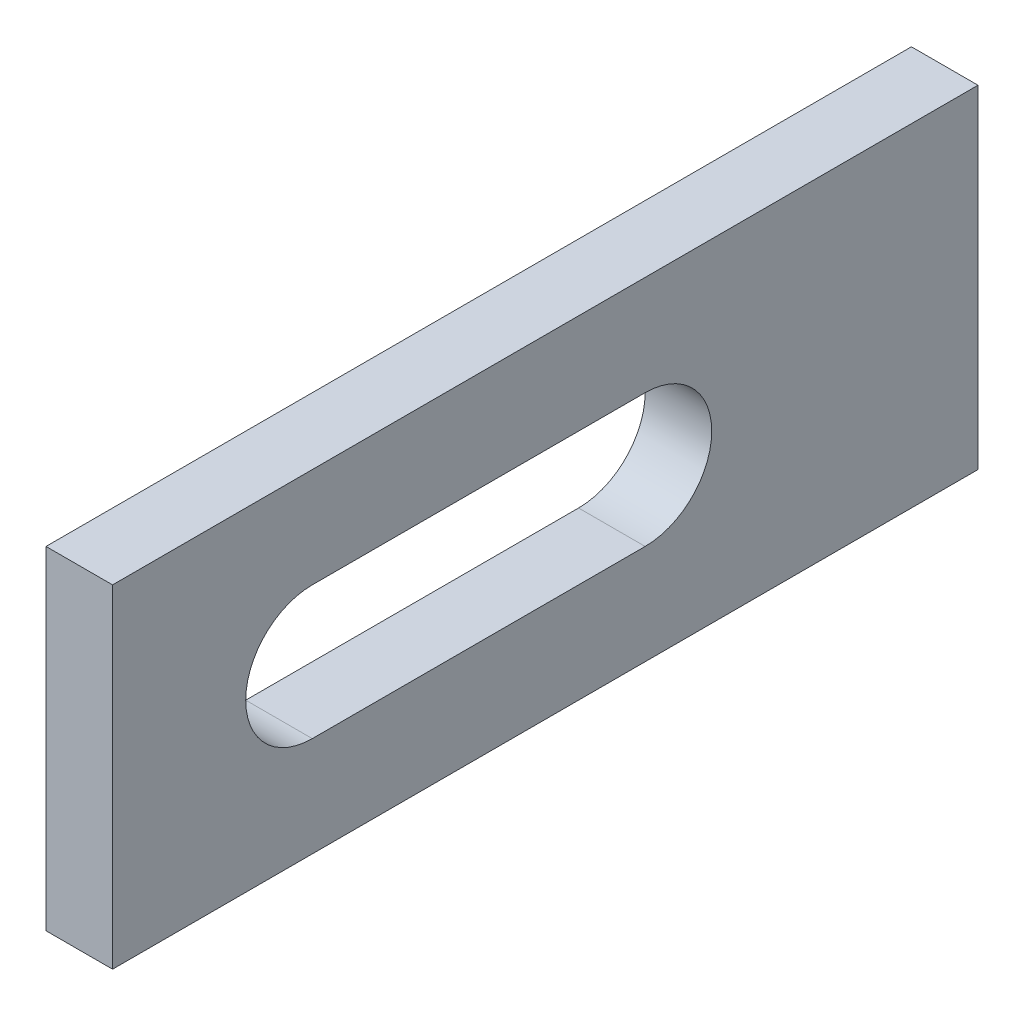
SolidWorks part; units mm, degrees
material "1.0038 (S235JRG2)"
ref_plane "Plan de face" through (0, 0, 0) normal (0, 0, 1) x (1, 0, 0)
ref_plane "Plan de dessus" through (0, 0, 0) normal (0, 1, 0) x (1, 0, 0)
ref_plane "Plan de droite" through (0, 0, 0) normal (1, 0, 0) x (0, 0, -1)
sketch "Esquisse1" plane through (0, 0, 0) normal (0, 0, 1) x (1, 0, 0)
  line L1 (-5, -25) -> (5, -25)
  line L2 (-5, -25) -> (-5, 25)
  line L3 (-5, 25) -> (5, 25)
  line L4 (5, -25) -> (5, 25)
  point P4 (0, -25)
  point P5 (-5, 0)
  dimension "D1" = 50
  dimension "D2" = 10
extrude "Boss.-Extru.1" add sketch "Esquisse1" along normal mid plane 130
sketch "Esquisse2" plane through (5, 0, 0) normal (1, 0, 0) x (0, 0, -1)
  line L0 (-65, -25) -> (-65, 25) construction
  line L2 (-35, 10) -> (15, 10)
  line L4 (15, -10) -> (-35, -10)
  line L6 (-65, 25) -> (65, 25) construction
  arc A0 (-35, 10) -> (-35, -10) centre (-35, 0) ccw
  arc A1 (15, -10) -> (15, 10) centre (15, 0) ccw
  dimension "D1" = 30
  dimension "D2" = 50
  dimension "D3" = 20
  dimension "D4" = 20
  dimension "D5" = 25
extrude "Enlèv. mat.-Extru.1" cut sketch "Esquisse2" against normal blind 110
